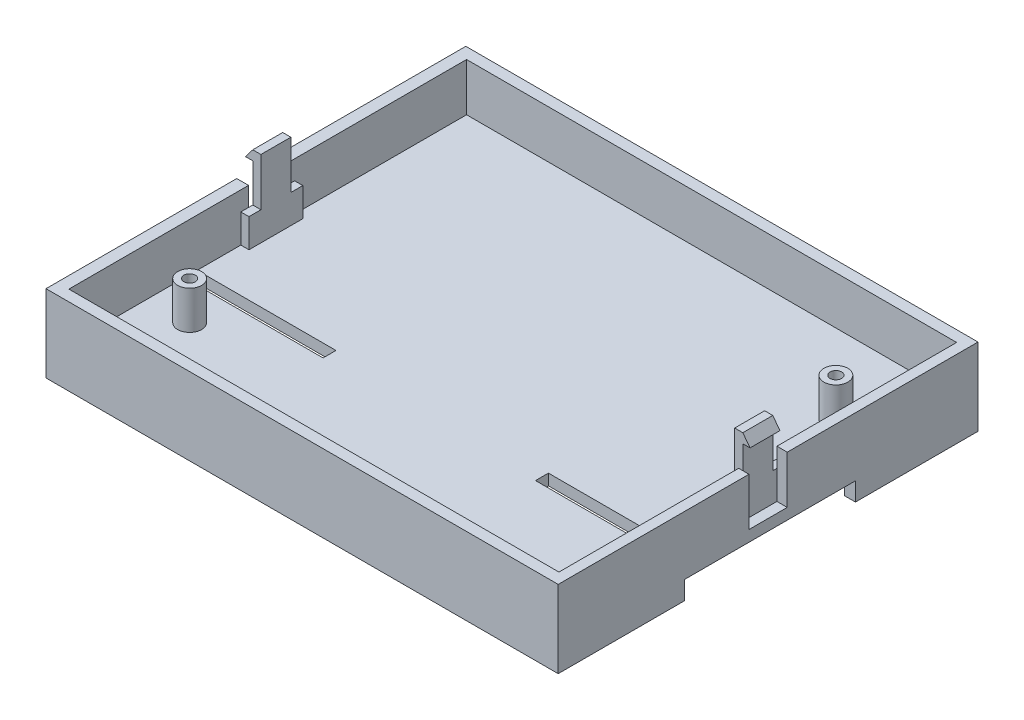
SolidWorks part; units mm, degrees
material "ABS"
ref_plane "Alzado" through (0, 0, 0) normal (0, 0, 1) x (1, 0, 0)
ref_plane "Planta" through (0, 0, 0) normal (0, 1, 0) x (1, 0, 0)
ref_plane "Vista lateral" through (0, 0, 0) normal (1, 0, 0) x (0, 0, -1)
sketch "Sketch1" plane through (0, 0, 0) normal (0, 1, 0) x (1, 0, 0)
  line L1 (0, 0) -> (107, 0)
  line L2 (0, 0) -> (0, 87.7)
  line L3 (0, 87.7) -> (107, 87.7)
  line L4 (107, 0) -> (107, 87.7)
  dimension "D1" = 107
  dimension "D2" = 87.7
extrude "Boss-Extrude1" add sketch "Sketch1" along normal blind 2.31
sketch "Sketch2" plane through (0, 2.31, 0) normal (0, 1, 0) x (1, 0, 0)
  line L1 (0, 47.85) -> (2.4669, 47.85)
  line L2 (0, 87.7) -> (107, 87.7)
  line L3 (0, 87.7) -> (0, 47.85)
  line L4 (0, 0) -> (107, 0)
  line L6 (107, 87.7) -> (107, 47.85)
  line L7 (2.4669, 2.31) -> (104.8469, 2.31)
  line L8 (2.4669, 2.31) -> (2.4669, 39.85)
  line L9 (2.4669, 85.39) -> (104.8469, 85.39)
  line L10 (104.8469, 2.31) -> (104.8469, 39.85)
  line L11 (0, 39.85) -> (2.4669, 39.85)
  line L12 (2.4669, 47.85) -> (2.4669, 85.39)
  line L14 (0, 39.85) -> (0, 0)
  line L15 (107, 39.85) -> (107, 0)
  line L17 (104.8469, 47.85) -> (104.8469, 85.39)
  line L18 (104.8469, 47.85) -> (107, 47.85)
  line L19 (104.8469, 39.85) -> (107, 39.85)
  point P17 (0, 0)
  dimension "D1" = 39.85
  dimension "D2" = 39.85
  dimension "D3" = 2.31
  dimension "D4" = 37.54
  dimension "D5" = 102.38
extrude "Boss-Extrude2" add sketch "Sketch2" along normal blind 10
sketch "Sketch3" plane through (0, 2.31, 0) normal (0, 1, 0) x (1, 0, 0)
  line L0 (2.4669, 2.31) -> (2.4669, 39.85) construction
  line L1 (104.8469, 85.39) -> (104.8469, 47.85) construction
  line L2 (104.8469, 2.31) -> (2.4669, 2.31) construction
  line L3 (2.4669, 85.39) -> (104.8469, 85.39) construction
  circle A0 centre (11.1569, 18.85) radius 1.2
  circle A1 centre (96.1569, 68.85) radius 1.2
  circle A2 centre (11.1569, 18.85) radius 2.5
  circle A3 centre (96.1569, 68.85) radius 2.5
  dimension "D1" = 8.69
  dimension "D5" = 2.4
  dimension "D6" = 2.4
  dimension "D7" = 5
  dimension "D8" = 5
  dimension "D2" = 8.69
  dimension "D3" = 16.54
  dimension "D4" = 16.54
extrude "Boss-Extrude3" add sketch "Sketch3" along normal blind 8
sketch "Sketch4" plane through (0, 0, 0) normal (0, -1, 0) x (-1, 0, 0)
  line L0 (-47.32, 0) -> (-47.32, 2.31)
  line L1 (0, 87.7) -> (-47.32, 87.7)
  line L2 (0, 87.7) -> (0, 62.1)
  line L3 (0, 0) -> (-107, 0)
  line L4 (-107, 87.7) -> (-107, 62.1)
  line L5 (-2.31, 85.39) -> (-43.3322, 85.39)
  line L6 (-2.31, 85.39) -> (-2.31, 62.1)
  line L7 (-2.31, 2.31) -> (-104.69, 2.31)
  line L8 (-104.69, 85.39) -> (-104.69, 62.1)
  line L9 (-59.68, 0) -> (-59.68, 2.31)
  line L10 (-63.6678, 85.39) -> (-104.69, 85.39)
  line L11 (-59.68, 87.7) -> (-107, 87.7)
  line L12 (-97.69, 62.1) -> (-59.68, 62.1)
  line L13 (-63.6678, 85.39) -> (-63.6678, 64.41)
  line L14 (-43.3322, 85.39) -> (-43.3322, 64.41)
  line L15 (-97.69, 64.41) -> (-63.6678, 64.41)
  line L16 (-43.3322, 64.41) -> (-9.31, 64.41)
  line L17 (-47.32, 62.1) -> (-9.31, 62.1)
  line L18 (-47.32, 62.1) -> (-47.32, 87.7)
  line L19 (-59.68, 62.1) -> (-59.68, 87.7)
  line L20 (-97.69, 64.41) -> (-97.69, 62.1)
  line L21 (-9.31, 64.41) -> (-9.31, 62.1)
  line L22 (-104.69, 62.1) -> (-107, 62.1)
  line L23 (-2.31, 62.1) -> (0, 62.1)
  line L24 (-107, 26.416) -> (-102.9106, 26.416)
  line L25 (-104.69, 24.6112) -> (-104.69, 2.31)
  line L26 (-107, 26.416) -> (-107, 0)
  line L27 (-2.31, 24.6112) -> (-2.31, 2.31)
  line L28 (0, 26.416) -> (0, 0)
  line L29 (-104.69, 24.6112) -> (-77.0026, 24.6112)
  line L30 (-29.9974, 0) -> (-29.9974, 2.31)
  line L31 (-77.0026, 0) -> (-77.0026, 2.31)
  line L32 (-102.9106, 29.1084) -> (-77.0026, 29.1084)
  line L34 (-102.9106, 26.416) -> (-102.9106, 29.1084)
  line L35 (-4.0894, 26.416) -> (-4.0894, 29.1084)
  line L36 (0, 87.7) -> (0, 0) construction
  line L37 (-77.0026, 26.416) -> (-77.0026, 29.1084)
  line L38 (-29.9974, 26.416) -> (-29.9974, 29.1084)
  line L39 (-29.9974, 24.6112) -> (-2.31, 24.6112)
  line L40 (-4.0894, 26.416) -> (0, 26.416)
  line L41 (-29.9974, 29.1084) -> (-4.0894, 29.1084)
  line L42 (-77.0026, 24.6112) -> (-77.0026, 26.416)
  line L43 (-29.9974, 24.6112) -> (-29.9974, 26.416)
  line M27 (0, 0) -> (0, 87.7)
  line M29 (-107, 87.7) -> (-107, 0)
  line M30 (-107, 0) -> (0, 0)
  dimension "D1" = 2.31
  dimension "D2" = 2.31
  dimension "D3" = 41.0222
  dimension "D4" = 2.31
  dimension "D5" = 47.32
  dimension "D6" = 47.32
  dimension "D7" = 23.29
  dimension "D8" = 26.416
  dimension "D9" = 22.3012
  dimension "D10" = 2.31
  dimension "D11" = 29.9974
  dimension "D12" = 29.9974
  dimension "D13" = 29.1084
  dimension "D15" = 4.0894
extrude "Boss-Extrude4" add sketch "Sketch4" along normal blind 3.85 contours L29 L42 L37 L32 L34 L24 L31 L7 L25 M29 M30 | L43 L39 L27 L7 L30 L3 L40 L35 L41 L38 M27 | L17 L21 L16 L14 L5 L6 L23 L2 L1 L18 | L15 L13 L10 L8 L22 L4 L11 L19 L12 L20
sketch "Sketch5" plane through (0, 2.31, 0) normal (0, 1, 0) x (1, 0, 0)
  line L0 (104.8469, 2.31) -> (2.4669, 2.31) construction
  line L1 (3.4669, 29.11) -> (31.4669, 29.11)
  line L2 (3.4669, 29.11) -> (3.4669, 26.41)
  line L3 (3.4669, 26.41) -> (31.4669, 26.41)
  line L4 (31.4669, 29.11) -> (31.4669, 26.41)
  line L5 (75.8469, 29.11) -> (103.8469, 29.11)
  line L6 (75.8469, 29.11) -> (75.8469, 26.41)
  line L7 (75.8469, 26.41) -> (103.8469, 26.41)
  line L8 (103.8469, 29.11) -> (103.8469, 26.41)
  line L9 (104.8469, 2.31) -> (2.4669, 2.31) construction
  line L10 (2.4669, 2.31) -> (2.4669, 39.85) construction
  line L11 (104.8469, 39.85) -> (104.8469, 2.31) construction
  dimension "D1" = 28
  dimension "D2" = 28
  dimension "D3" = 2.7
  dimension "D4" = 2.7
  dimension "D5" = 26.8
  dimension "D6" = 26.8
  dimension "D7" = 1
  dimension "D8" = 1
extrude "Cut-Extrude1" cut sketch "Sketch5" against normal blind 3.85
sketch "Sketch6" plane through (102.9106, 0, 0) normal (1, 0, 0) x (0, 0, -1)
  line L0 (29.1084, -3.85) -> (26.416, -1.54)
  line L2 (26.416, -3.85) -> (26.416, 0) construction
  line L3 (26.416, -3.85) -> (26.416, -1.54) construction
  line L4 (26.416, -1.54) -> (29.1084, -1.54)
  line L5 (29.1084, -1.54) -> (26.416, -1.54) construction
  line L6 (29.1084, -3.85) -> (29.1084, -1.54) construction
  line L7 (29.1084, -1.54) -> (29.1084, -3.85)
extrude "Cut-Extrude2" cut sketch "Sketch6" against normal blind 107
sketch "Sketch7" plane through (0, 2.31, 0) normal (0, 1, 0) x (1, 0, 0)
  line L0 (2.4669, 47.85) -> (2.4669, 85.39) construction
  line L1 (2.4669, 49.48) -> (4.1669, 49.48)
  line L2 (2.4669, 49.48) -> (2.4669, 38.23)
  line L3 (2.4669, 38.23) -> (4.1669, 38.23)
  line L4 (4.1669, 49.48) -> (4.1669, 38.23)
  line L5 (104.8469, 85.39) -> (104.8469, 47.85) construction
  line L6 (104.8469, 49.48) -> (103.1469, 49.48)
  line L7 (104.8469, 49.48) -> (104.8469, 38.23)
  line L8 (104.8469, 38.23) -> (103.1469, 38.23)
  line L9 (103.1469, 49.48) -> (103.1469, 38.23)
  line L10 (104.8469, 2.31) -> (2.4669, 2.31) construction
  dimension "D1" = 11.25
  dimension "D2" = 11.25
  dimension "D3" = 1.7
  dimension "D4" = 1.7
  dimension "D5" = 35.92
  dimension "D6" = 35.92
extrude "Boss-Extrude5" add sketch "Sketch7" along normal blind 16
sketch "Sketch8" plane through (104.8469, 0, 0) normal (1, 0, 0) x (0, 0, -1)
  line L1 (38.23, 18.31) -> (40.73, 18.31)
  line L2 (38.23, 18.31) -> (38.23, 8.31)
  line L3 (38.23, 8.31) -> (40.73, 8.31)
  line L4 (40.73, 18.31) -> (40.73, 8.31)
  line L5 (49.48, 18.31) -> (46.98, 18.31)
  line L6 (49.48, 18.31) -> (49.48, 8.31)
  line L7 (49.48, 8.31) -> (46.98, 8.31)
  line L8 (46.98, 18.31) -> (46.98, 8.31)
  dimension "D1" = 6.25
  dimension "D2" = 2.5
  dimension "D3" = 10
  dimension "D4" = 10
extrude "Cut-Extrude3" cut sketch "Sketch8" against normal blind 102.38
sketch "Sketch9" plane through (0, 0, -40.73) normal (0, 0, 1) x (1, 0, 0)
  line L0 (104.8469, 18.31) -> (106.3469, 16.31)
  line L1 (106.3469, 16.31) -> (104.8469, 16.31)
  line L2 (104.8469, 8.31) -> (104.8469, 18.31) construction
  line L3 (104.8469, 16.31) -> (104.8469, 18.31)
  dimension "D1" = 2
  dimension "D2" = 1.5
extrude "Boss-Extrude6" add sketch "Sketch9" against normal blind 6.25
sketch "Sketch10" plane through (0, 0, -40.73) normal (0, 0, 1) x (1, 0, 0)
  line L0 (2.4669, 16.31) -> (0.9669, 16.31)
  line L1 (2.4669, 8.31) -> (2.4669, 18.31) construction
  line L2 (0.9669, 16.31) -> (2.4669, 18.31)
  line L3 (2.4669, 18.31) -> (2.4669, 16.31)
  line L4 (2.4669, 16.31) -> (2.7876, 16.2446)
  line M5 (2.4669, 18.31) -> (2.4669, 8.31)
  dimension "D1" = 2
  dimension "D2" = 1.5
extrude "Boss-Extrude7" add sketch "Sketch10" against normal blind 6.25 contours L2 L0 M5
